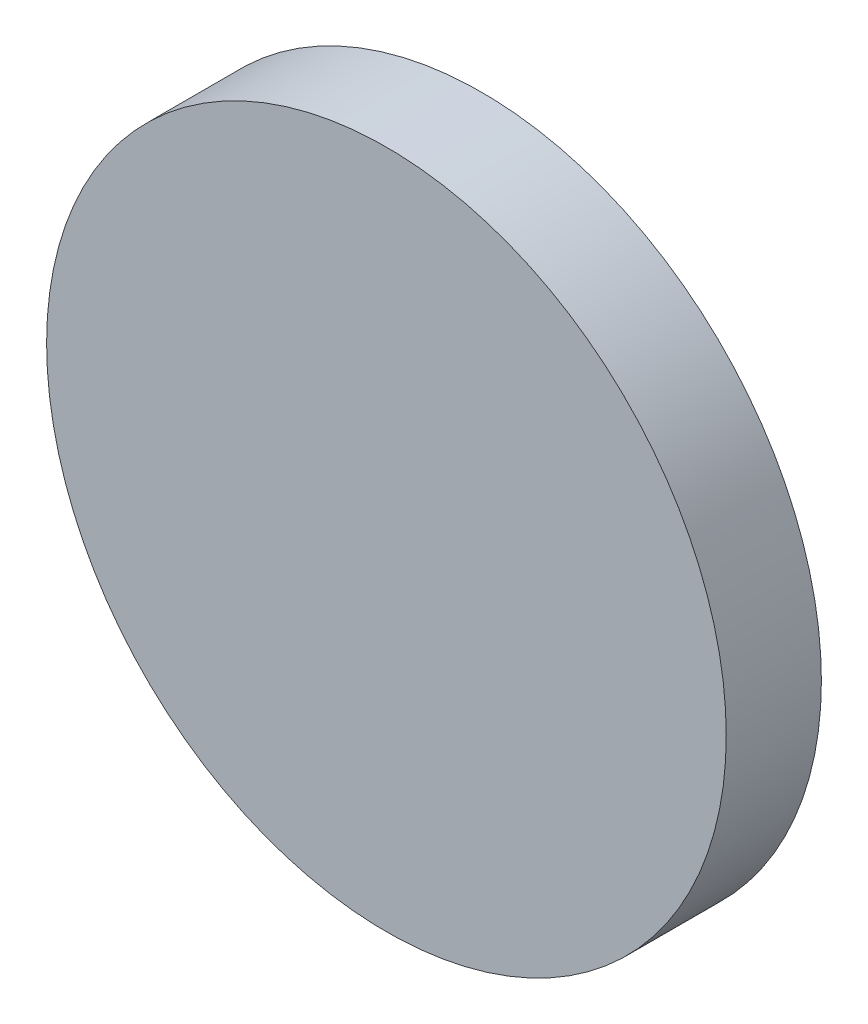
SolidWorks part; units mm, degrees
material "Glass"
ref_plane "Front Plane" through (0, 0, 0) normal (0, 0, 1) x (1, 0, 0)
ref_plane "Top Plane" through (0, 0, 0) normal (0, 1, 0) x (1, 0, 0)
ref_plane "Right Plane" through (0, 0, 0) normal (1, 0, 0) x (0, 0, -1)
sketch "Sketch1" plane through (0, 0, 0) normal (0, 0, 1) x (1, 0, 0)
  circle A0 centre (0, 0) radius 12.5
  dimension "D1" = 25
extrude "Boss-Extrude1" add sketch "Sketch1" along normal blind 3.5
